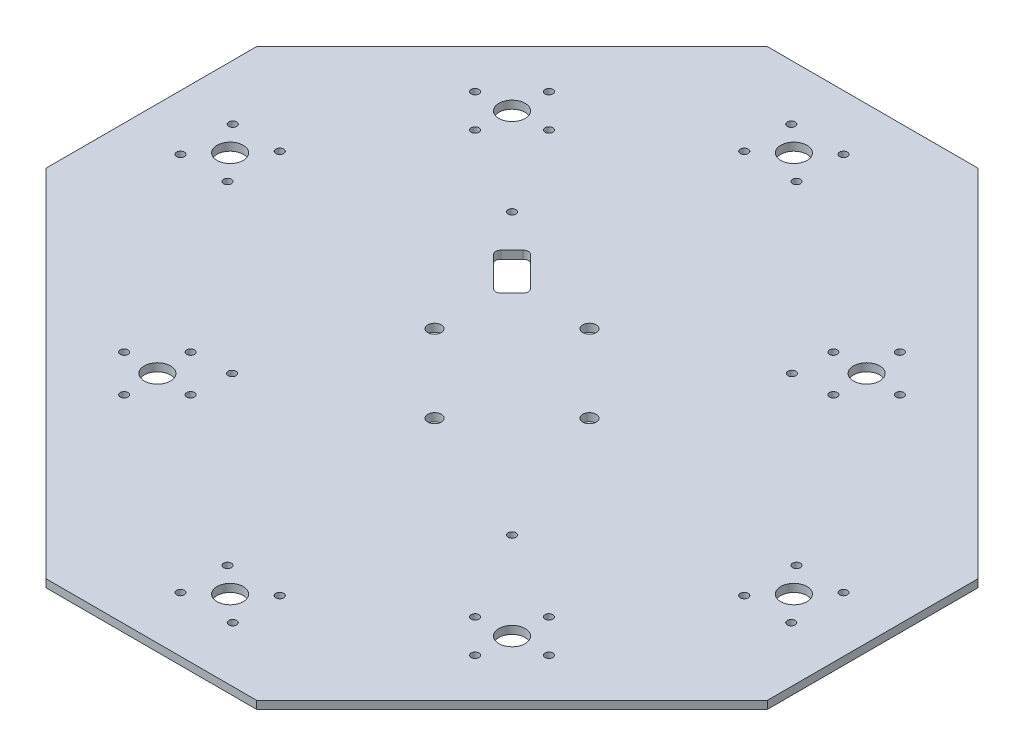
SolidWorks part; units mm, degrees
ref_plane "Front Plane" through (0, 0, 0) normal (0, 0, 1) x (1, 0, 0)
ref_plane "Top Plane" through (0, 0, 0) normal (0, 1, 0) x (1, 0, 0)
ref_plane "Right Plane" through (0, 0, 0) normal (1, 0, 0) x (0, 0, -1)
sketch "Sketch1" plane through (0, 0, 0) normal (0, 1, 0) x (1, 0, 0)
  line L0 (0, 0) -> (-88.7419, -88.7419) construction
  line L1 (68.75, -165.9772) -> (165.9772, -68.75) construction
  line L2 (165.9772, -68.75) -> (165.9772, 68.75) construction
  line L3 (165.9772, 68.75) -> (68.75, 165.9772) construction
  line L4 (68.75, 165.9772) -> (-68.75, 165.9772) construction
  line L5 (-68.75, 165.9772) -> (-165.9772, 68.75) construction
  line L6 (-165.9772, 68.75) -> (-165.9772, -68.75) construction
  line L7 (-165.9772, -68.75) -> (-68.75, -165.9772) construction
  line L8 (-68.75, -165.9772) -> (68.75, -165.9772) construction
  line L9 (117.3636, 117.3636) -> (-117.3636, -117.3636) construction
  line L10 (0, 0) -> (88.7419, 88.7419) construction
  line L11 (-88.7419, -88.7419) -> (-11.5066, -165.9772) construction
  line L12 (-11.5066, -165.9772) -> (-165.9772, -11.5066) construction
  line L13 (88.7419, 88.7419) -> (165.9772, 11.5066) construction
  line L14 (165.9772, 11.5066) -> (11.5066, 165.9772) construction
  circle A0 centre (0, 0) radius 165.9772 construction
  dimension "D1" = 137.5
sketch "Sketch3" plane through (0, 0, 0) normal (0, 1, 0) x (1, 0, 0)
  line L3 (146.9176, 30.5662) -> (11.5066, 165.9772)
  line L4 (11.5066, 165.9772) -> (-68.75, 165.9772)
  line L5 (-68.75, 165.9772) -> (-165.9772, 68.75)
  line L6 (-165.9772, 68.75) -> (-165.9772, -11.5066)
  line L7 (-165.9772, -11.5066) -> (-30.5662, -146.9176)
  line L8 (-68.75, 165.9772) -> (146.9176, -49.6904) construction
  line L9 (-165.9772, 68.75) -> (49.6904, -146.9176) construction
  line L10 (49.6904, -146.9176) -> (146.9176, -49.6904)
  line L11 (146.9176, 30.5662) -> (146.9176, -49.6904)
  line L12 (49.6904, -146.9176) -> (-30.5662, -146.9176)
extrude "Boss-Extrude2" add sketch "Sketch3" along normal blind 3
hole_wizard "13/64 (0.20313) Diameter Hole1" positions "Sketch8" profile "Sketch7" hole size "13/64" standard "ANSI Inch" end condition up to next
sketch "Sketch8" plane through (0, 0, 0) normal (0, -1, 0) x (-1, 0, 0)
  point P0 (39.0298, 9.5282)
  point P3 (9.5282, -19.9702)
  point P6 (-19.9702, 9.5314)
  point P9 (9.5314, 39.0298)
sketch "Sketch7" plane through (-39.0298, 0, -9.5282) normal (1, 0, 0) x (0, 0, -1)
  line L0 (0, 0) -> (0, 3)
  line L1 (0, 3) -> (2.5798, 3)
  line L2 (2.5798, 3) -> (2.5798, 0)
  line L5 (2.5798, 0) -> (0, 0)
  line L11 (0, -6.35) -> (0, 107.95) construction
  dimension "Thru Hole Dia." = 5.1595
  dimension "Thru Hole Depth" = 3
sketch "Sketch11" plane through (0, 0, 0) normal (0, -1, 0) x (-1, 0, 0)
  line L0 (98.2717, -79.2121) -> (-79.2121, 98.2717)
  line L1 (165.9772, -11.5066) -> (30.5662, -146.9176) construction
  line L2 (-146.9176, 30.5662) -> (-11.5066, 165.9772) construction
  line L3 (-79.2121, 98.2717) -> (9.5298, 9.5298)
  line L4 (9.5298, 9.5298) -> (36.0463, 36.0463)
sketch "Sketch12" plane through (0, 0, 0) normal (0, -1, 0) x (1, 0, 0)
  line L0 (-9.5298, -9.5298) -> (-36.0463, -36.0463) construction
  line L1 (-36.0463, -36.0463) -> (-39.5818, -32.5108)
  line L2 (-36.0463, -36.0463) -> (-32.5108, -39.5818)
  line L3 (-32.5108, -39.5818) -> (-46.6529, -53.724)
  line L4 (-46.6529, -53.724) -> (-53.724, -46.6529)
  line L5 (-53.724, -46.6529) -> (-39.5818, -32.5108)
extrude "Cut-Extrude1" cut sketch "Sketch12" against normal through all
fillet "Fillet2" radius 2 1 edges at (-39.5818, 1.5, -32.5108)
fillet "Fillet3" radius 2 1 edges at (-32.5108, 1.5, -39.5818)
fillet "Fillet4" radius 2 1 edges at (-53.724, 1.5, -46.6529)
fillet "Fillet5" radius 2 1 edges at (-46.6529, 1.5, -53.724)
hole_wizard "Ø3.0mm Dowel Hole1" positions "Sketch15" profile "Sketch16" hole size "Ø3.0" standard "ANSI Metric" end condition up to next
sketch "Sketch15" plane through (0, 0, 0) normal (0, -1, 0) x (-1, 0, 0)
  point P0 (-76.3832, -90.4563)
  point P3 (-90.4539, -76.3841)
  point P6 (-77.796, -63.7276)
  point P9 (-63.7253, -77.7997)
  point P12 (-19.5121, -125.8676)
  point P15 (-19.5121, -107.9676)
  point P18 (0.3879, -125.8676)
  point P21 (0.3879, -107.9676)
  point P24 (63.6953, -58.7041)
  point P27 (76.3518, -71.362)
  point P30 (90.424, -57.2914)
  point P33 (77.7675, -44.6335)
  point P36 (144.9272, 38.5717)
  point P39 (127.0272, 38.5717)
  point P42 (127.0272, 18.6717)
  point P45 (144.9272, 18.6717)
  point P48 (96.8556, 82.7872)
  point P51 (82.785, 96.8594)
  point P54 (95.4429, 109.5159)
  point P57 (109.5135, 95.4437)
  point P60 (18.6717, 144.9272)
  point P63 (18.6717, 127.0272)
  point P66 (38.5717, 127.0272)
  point P69 (38.5717, 144.9272)
  point P72 (-58.7079, 63.6931)
  point P75 (-71.3644, 76.351)
  point P78 (-44.6357, 77.7637)
  point P81 (-57.2922, 90.4216)
  point P84 (-125.8676, -19.5121)
  point P87 (-107.9676, -19.5121)
  point P90 (-107.9676, 0.3879)
  point P93 (-125.8676, 0.3879)
sketch "Sketch16" plane through (76.3832, 0, 90.4563) normal (1, 0, 0) x (0, 0, -1)
  line L0 (0, 0) -> (0, 3)
  line L1 (0, 3) -> (1.5, 3)
  line L2 (1.5, 3) -> (1.5, 0)
  line L5 (1.5, 0) -> (0, 0)
  line L11 (0, -6.35) -> (0, 107.95) construction
  dimension "Thru Hole Dia." = 3
  dimension "Thru Hole Depth" = 3
hole_wizard "Ø10.0mm Dowel Hole1" positions "Sketch18" profile "Sketch17" hole size "Ø10.0" standard "ANSI Metric" end condition up to next
sketch "Sketch18" plane through (0, 3, 0) normal (0, 1, 0) x (1, 0, 0)
  point P0 (-135.9772, 28.6217)
  point P3 (-96.1492, 96.1515)
  point P6 (-28.6217, 135.9772)
  point P9 (58, 77.0574)
  point P12 (116.9176, -9.5621)
sketch "Sketch17" plane through (-135.9772, 3, -28.6217) normal (1, 0, 0) x (0, 0, 1)
  line L0 (0, 0) -> (0, 3)
  line L1 (0, 3) -> (5, 3)
  line L2 (5, 3) -> (5, 0)
  line L5 (5, 0) -> (0, 0)
  line L11 (0, -6.35) -> (0, 107.95) construction
  dimension "Thru Hole Dia." = 10
  dimension "Thru Hole Depth" = 3
hole_wizard "Ø10.0mm Dowel Hole2" positions "Sketch19" profile "Sketch20" hole size "Ø10.0" standard "ANSI Metric" end condition up to next
sketch "Sketch19" plane through (0, 3, 0) normal (0, 1, 0) x (1, 0, 0)
  point P0 (9.5621, -116.9176)
  point P3 (77.0896, -77.0919)
  point P6 (-77.0597, -57.9977)
sketch "Sketch20" plane through (9.5621, 3, 116.9176) normal (1, 0, 0) x (0, 0, 1)
  line L0 (0, 0) -> (0, 3)
  line L1 (0, 3) -> (5, 3)
  line L2 (5, 3) -> (5, 0)
  line L5 (5, 0) -> (0, 0)
  line L11 (0, -6.35) -> (0, 107.95) construction
  dimension "Thru Hole Dia." = 10
  dimension "Thru Hole Depth" = 3
hole_wizard "Ø3.0mm Dowel Hole2" positions "Sketch21" profile "Sketch22" hole size "Ø3.0" standard "ANSI Metric" end condition up to next
sketch "Sketch21" plane through (0, 0, 0) normal (0, -1, 0) x (-1, 0, 0)
  point P0 (62.8254, -43.771)
  point P3 (-43.771, -43.7658)
  point P6 (62.8306, 62.8254)
  point P9 (-43.7658, 62.8306)
sketch "Sketch22" plane through (-62.8254, 0, 43.771) normal (1, 0, 0) x (0, 0, -1)
  line L0 (0, 0) -> (0, 3)
  line L1 (0, 3) -> (1.5, 3)
  line L2 (1.5, 3) -> (1.5, 0)
  line L5 (1.5, 0) -> (0, 0)
  line L11 (0, -6.35) -> (0, 107.95) construction
  dimension "Thru Hole Dia." = 3
  dimension "Thru Hole Depth" = 3
